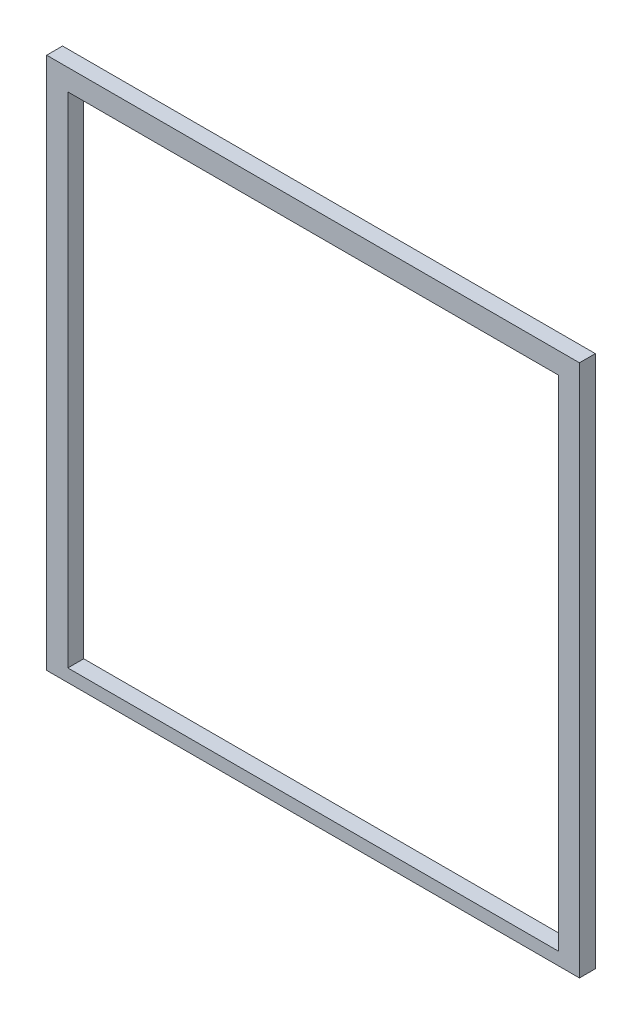
SolidWorks part; units mm, degrees
ref_plane "Front Plane" through (0, 0, 0) normal (0, 0, 1) x (1, 0, 0)
ref_plane "Top Plane" through (0, 0, 0) normal (0, 1, 0) x (1, 0, 0)
ref_plane "Right Plane" through (0, 0, 0) normal (1, 0, 0) x (0, 0, -1)
sketch "Sketch1" plane through (0, 0, 0) normal (0, 0, 1) x (1, 0, 0)
  line L1 (0, 0) -> (503, 0)
  line L2 (0, 0) -> (0, 503)
  line L3 (0, 503) -> (503, 503)
  line L4 (503, 0) -> (503, 503)
  line L5 (20, 483) -> (483, 483)
  line L6 (20, 483) -> (20, 12)
  line L7 (20, 12) -> (483, 12)
  line L8 (483, 483) -> (483, 12)
  dimension "D1" = 503
  dimension "D2" = 503
  dimension "D3" = 20
  dimension "D4" = 20
  dimension "D5" = 20
  dimension "D6" = 12
extrude "Boss-Extrude1" add sketch "Sketch1" along normal blind 15
